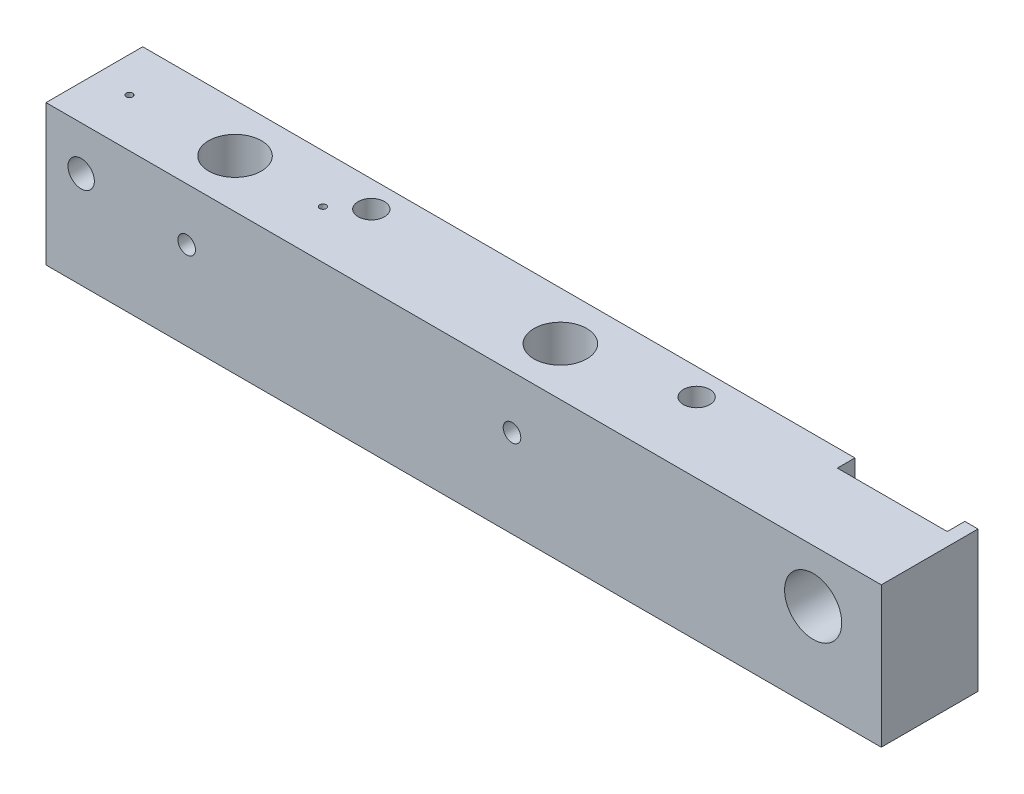
SolidWorks part; units mm, degrees
ref_plane "Front Plane" through (0, 0, 0) normal (0, 0, 1) x (1, 0, 0)
ref_plane "Top Plane" through (0, 0, 0) normal (0, 1, 0) x (1, 0, 0)
ref_plane "Right Plane" through (0, 0, 0) normal (1, 0, 0) x (0, 0, -1)
sketch "Sketch2" plane through (0, 0, 0) normal (0, 1, 0) x (1, 0, 0)
  line L1 (95, -11) -> (-95, -11)
  line L2 (95, -11) -> (95, 11)
  line L3 (95, 11) -> (-95, 11)
  line L4 (-95, -11) -> (-95, 11)
  line L5 (95, -11) -> (-95, 11) construction
  line L6 (95, 11) -> (-95, -11) construction
  point P0 (0, 0)
  dimension "D1" = 190
  dimension "22" = 22
extrude "Boss-Extrude1" add sketch "Sketch2" along normal blind 32
sketch "Sketch3" plane through (0, 32, 0) normal (0, 1, 0) x (1, 0, 0)
  line L1 (92, 7) -> (67, 7)
  line L2 (92, 7) -> (92, 11)
  line L3 (92, 11) -> (67, 11)
  line L4 (67, 7) -> (67, 11)
  line L5 (92, 7) -> (67, 11) construction
  line L6 (92, 11) -> (67, 7) construction
  line L7 (95, 11) -> (-95, 11) construction
  line L8 (-95, 11) -> (-95, -11) construction
  line L9 (95, -11) -> (95, 11) construction
  circle A0 centre (-87, 0) radius 0.75
  circle A1 centre (-63, 0) radius 6
  circle A2 centre (-37, 5) radius 3
  circle A3 centre (-43, 0) radius 0.75
  circle A4 centre (11, 0) radius 6
  circle A5 centre (37, 5) radius 3
  point P12 (79.5, 9)
  point P17 (0, 0)
  point P21 (0, 0)
  point P27 (0, 0)
  dimension "D1" = 12
  dimension "D2" = 6
  dimension "D3" = 6
  dimension "D4" = 12
  dimension "D5" = 1.5
  dimension "D6" = 1.5
  dimension "D8" = 24
  dimension "D9" = 58
  dimension "D10" = 6
  dimension "D11" = 20
  dimension "D12" = 74
  dimension "D13" = 74
  dimension "D14" = 56
  dimension "D15" = 25
  dimension "D16" = 3
  dimension "D17" = 4
extrude "Cut-Extrude1" cut sketch "Sketch3" against normal blind 24
sketch "Sketch4" plane through (0, 8, 0) normal (0, 1, 0) x (1, 0, 0)
  line L4 (67, 11) -> (67, 7)
  line L5 (67, 7) -> (92, 7)
  line L6 (92, 7) -> (92, 11)
  line L7 (92, 11) -> (67, 11)
  line L8 (67, 11) -> (67, 7)
  line L9 (67, 7) -> (92, 7)
  line L10 (92, 7) -> (92, 11)
  line L11 (92, 11) -> (67, 11)
  dimension "D1" = 0
extrude "Cut-Extrude2" cut sketch "Sketch4" against normal through all
sketch "Sketch5" plane through (0, 0, 11) normal (0, 0, 1) x (1, 0, 0)
  line L0 (-95, 0) -> (95, 0) construction
  line L1 (95, 32) -> (95, 0) construction
  circle A0 centre (-87, 22) radius 3
  circle A1 centre (-63, 20) radius 2
  circle A2 centre (11, 20) radius 2
  circle A3 centre (79.5, 20) radius 6.5
  point P10 (0, 0)
  point P11 (11.6489, 15.0446)
  point P13 (0, 0)
  point P17 (0, 0)
  point P19 (0, 0)
  dimension "D1" = 6
  dimension "D2" = 4
  dimension "D3" = 4
  dimension "D4" = 13
  dimension "D5" = 20
  dimension "D6" = 22
  dimension "D7" = 15.5
extrude "Cut-Extrude3" cut sketch "Sketch5" against normal blind 24
